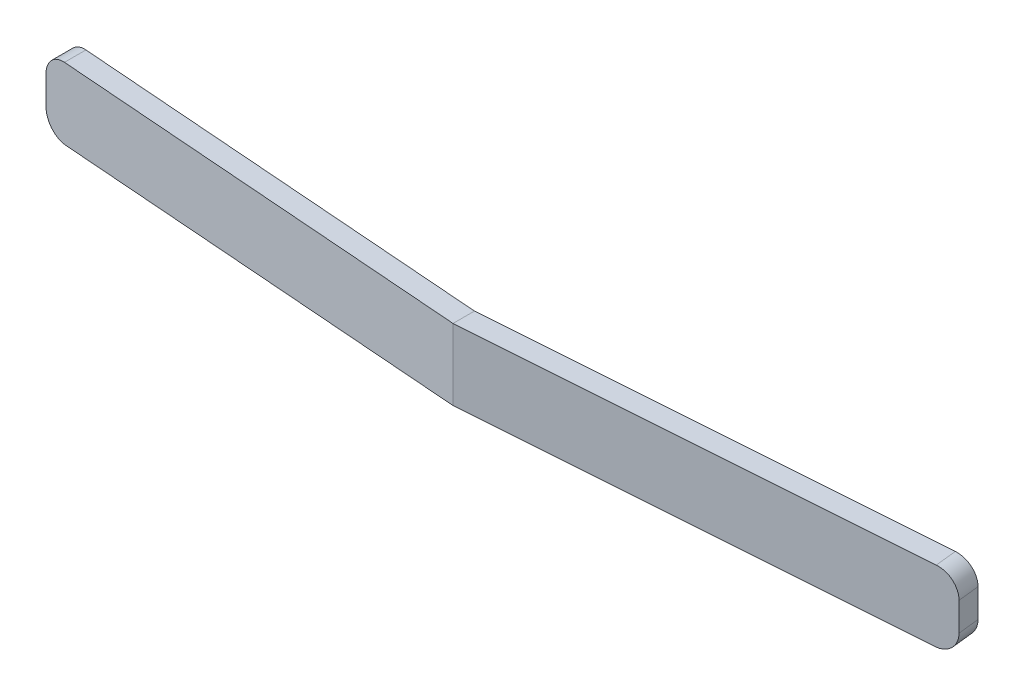
SolidWorks part; units mm, degrees
ref_plane "Front Plane" through (0, 0, 0) normal (0, 0, 1) x (1, 0, 0)
ref_plane "Top Plane" through (0, 0, 0) normal (0, 1, 0) x (1, 0, 0)
ref_plane "Right Plane" through (0, 0, 0) normal (1, 0, 0) x (0, 0, -1)
sketch "Sketch2" plane through (0, 0, 0) normal (0, 1, 0) x (1, 0, 0)
  line L0 (0, 31.0618) -> (0, -32.2351) construction
  line L1 (0, 0) -> (-64, 6.7831)
  line L2 (-64, 6.7831) -> (-64, 3.7663)
  line L3 (-64, 3.7663) -> (0, -3.0168)
  line L4 (0, -3.0168) -> (64.3162, 3.7999)
  line L5 (64.3162, 3.7999) -> (64, 6.7831)
  line L6 (64, 6.7831) -> (0, 0)
  point P9 (0, 0)
  dimension "D1" = 3
  dimension "D2" = 3
  dimension "D3" = 167.9
  dimension "D4" = 128
  dimension "D5" = 64
extrude "Boss-Extrude2" add sketch "Sketch2" along normal blind 20
sketch "Sketch3" plane through (0, 0, 0) normal (0, 0, 1) x (1, 0, 0)
  line L0 (-64, 15.7989) -> (-64, 5.7989)
  line L1 (-64, 20) -> (-64, 0) construction
  line L2 (-64, 5.7989) -> (0, 7.8909)
  line L3 (0, 20) -> (0, 0) construction
  line L4 (0, 7.8909) -> (64.3162, 5.8385)
  line L5 (64.3162, 20) -> (64.3162, 0) construction
  line L6 (64.3162, 5.8385) -> (64.3162, 15.8385)
  line L7 (64.3162, 15.8385) -> (0, 17.8909)
  line L8 (0, 17.8909) -> (-64, 15.7989)
  line L9 (0, 0) -> (64.3162, 0) construction
  line L10 (-64, 20) -> (64.3162, 20)
  line L11 (-64, 20) -> (-64, 0)
  line L12 (-64, 0) -> (64.3162, 0)
  line L13 (64.3162, 20) -> (64.3162, 0)
  dimension "D1" = 10
  dimension "D2" = 10
  dimension "D3" = 9.9947
  dimension "D4" = 176.3
extrude "Cut-Extrude1" cut sketch "Sketch3" along normal through all both and the other way through all contours L13 L4 L2 L11 L12 | L13 L10 L11 L8 L7
fillet "Fillet1" radius 3 4 edges at (-64, 5.7989, -5.2747) (-64, 15.7989, -5.2747) (64.1581, 5.8436, -5.2915) (64.1581, 15.8436, -5.2915)
